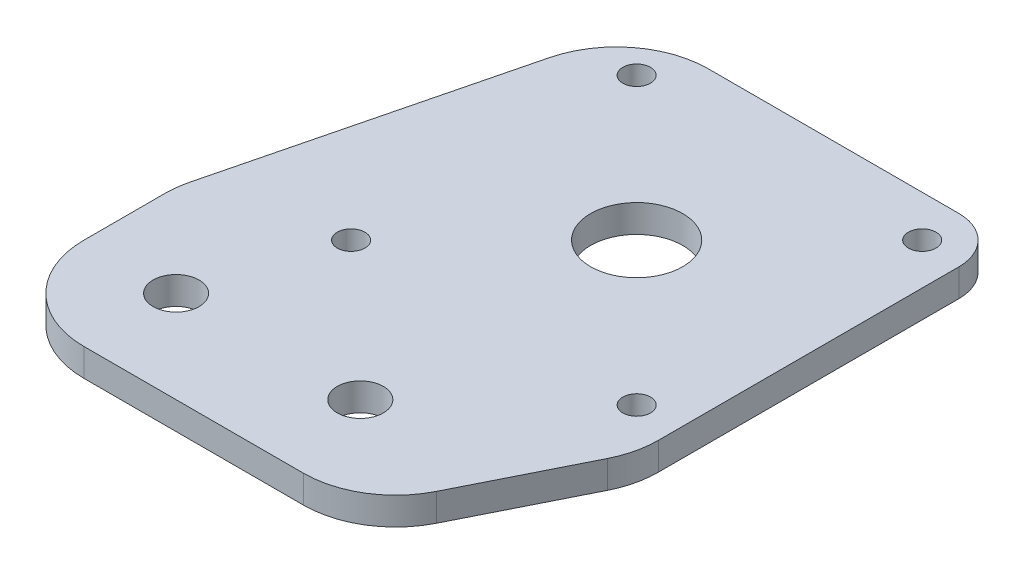
SolidWorks part; units mm, degrees
ref_plane "Front Plane" through (0, 0, 0) normal (0, 0, 1) x (1, 0, 0)
ref_plane "Top Plane" through (0, 0, 0) normal (0, 1, 0) x (1, 0, 0)
ref_plane "Right Plane" through (0, 0, 0) normal (1, 0, 0) x (0, 0, -1)
sketch "Sketch1" plane through (0, 0, 0) normal (0, 1, 0) x (1, 0, 0)
  line L0 (20, -20) -> (10, -40)
  line L1 (-20, 20) -> (20, 20)
  line L2 (-30, -20) -> (-30, -40)
  line L3 (-30, -40) -> (10, -40)
  line L4 (20, 20) -> (20, -20)
  line L5 (-20, 20) -> (-30, -20)
  circle A0 centre (0, 0) radius 5
  dimension "D1" = 10
  dimension "D4" = 20
  dimension "D2" = 50
  dimension "D3" = 60
  dimension "D5" = 30
  dimension "D6" = 40
  dimension "D7" = 40
  dimension "D8" = 40
  dimension "D9" = 20
extrude "Boss-Extrude1" add sketch "Sketch1" along normal blind 3
sketch "Sketch2" plane through (0, 3, 0) normal (0, 1, 0) x (1, 0, 0)
  line L0 (0, 0) -> (39.7425, 0) construction
  line L1 (39.7425, 0) -> (0, 0) construction
  line L2 (0, 0) -> (0, 21.3561) construction
  circle A0 centre (-15.5, 15.5) radius 1.5
  dimension "D1" = 3
  dimension "D2" = 15.5
  dimension "D3" = 15.5
extrude "Cut-Extrude1" cut sketch "Sketch2" against normal through all
pattern_linear "LPattern1" count 2 spacing 31 along (1, 0, 0) count 2 spacing 31 along (0, 0, 1) of "Cut-Extrude1"
sketch "Sketch3" plane through (0, 3, 0) normal (0, 1, 0) x (1, 0, 0)
  line L0 (-30, -40) -> (10, -40) construction
  line L1 (-30, -20) -> (-30, -40) construction
  circle A0 centre (-20, -30) radius 2.5
  dimension "D1" = 5
  dimension "D3" = 10
  dimension "D4" = 10
extrude "Cut-Extrude2" cut sketch "Sketch3" against normal through all
pattern_linear "LPattern2" count 2 spacing 20 along (1, 0, 0) of "Cut-Extrude2"
fillet "Fillet1" radius 10 5 edges at (-30, 1.5, 40) (10, 1.5, 40) (20, 1.5, 20) (-20, 1.5, -20) (-30, 1.5, 20)
fillet "Fillet2" radius 5 1 edges at (20, 1.5, -20)
